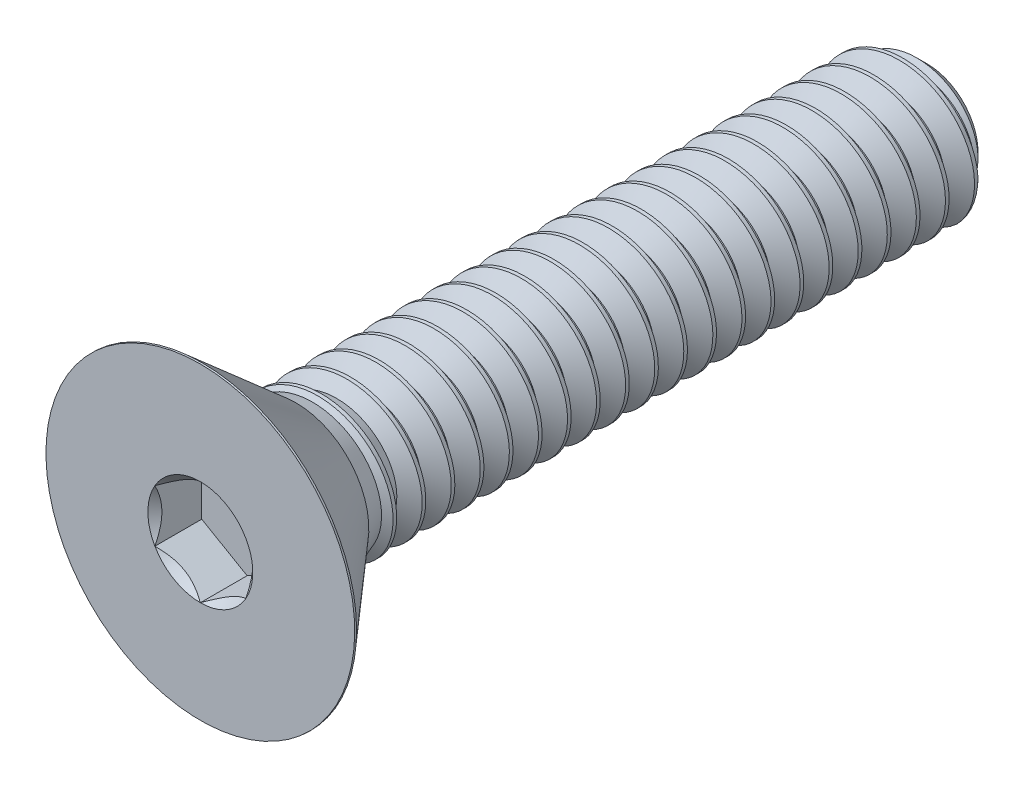
SolidWorks part; units mm, degrees
material "AISI 1020"
ref_plane "Front Plane" through (0, 0, 0) normal (0, 0, 1) x (1, 0, 0)
ref_plane "Top Plane" through (0, 0, 0) normal (0, 1, 0) x (1, 0, 0)
ref_plane "Right Plane" through (0, 0, 0) normal (1, 0, 0) x (0, 0, -1)
sketch "Sketch1" plane through (0, 0, 0) normal (1, 0, 0) x (0, 0, -1)
  line L0 (-15.875, 0) -> (15.875, 0) construction
  line L1 (-15.875, 0) -> (-15.875, 6.7437)
  line L2 (-15.875, 6.7437) -> (-15.7932, 6.7437)
  line L3 (-15.7932, 6.7437) -> (-11.7856, 3.2599)
  line L4 (-15.7932, -6.7437) -> (-11.7856, -3.2599)
  line L5 (15.875, 0) -> (15.875, 3.175)
  line L6 (15.875, 3.175) -> (-11.7856, 3.175)
  line L7 (14.9225, 3.175) -> (15.875, 2.2225)
  line L8 (15.7956, 3.3125) -> (16.4306, 2.2126) construction
  line L9 (16.4306, 2.2126) -> (17.0656, 3.3125) construction
  line L10 (17.0656, 3.3125) -> (15.7956, 3.3125) construction
  line L11 (15.8353, 3.2437) -> (17.0259, 3.2437)
  line L12 (17.0259, 3.2437) -> (16.51, 2.3501)
  line L13 (16.51, 2.3501) -> (16.3512, 2.3501)
  line L14 (16.3512, 2.3501) -> (15.8353, 3.2437)
  line L15 (16.4306, 2.3501) -> (16.4306, 2.2126) construction
  line L16 (15.875, 3.175) -> (16.9862, 3.175) construction
  line L17 (16.4306, 3.3125) -> (16.4306, 3.175) construction
  line L18 (15.875, -3.175) -> (-11.7856, -3.175)
  arc A0 (-11.7856, 3.2599) -> (-11.5584, 3.175) centre (-11.5584, 3.5213) ccw
  point P2 (0, 0)
  point P23 (-13.8303, 0)
  point P27 (16.4306, 3.2437)
  point P30 (13.97, -3.175)
  point P31 (-11.7856, 6.7437)
  point P33 (-11.7856, -6.7437)
  point P34 (-15.7932, -6.7437)
  dimension "Length" = 31.75
  dimension "Head Height" = 4.0894
  dimension "Head Diameter" = 13.4874
  dimension "Countersink Angle" = 82
  dimension "Screw Size Decimal Equivalent" = 6.35
  dimension "Pitch" = 1.27
  dimension "D4" = 0.1588
  dimension "D3" = 45
  dimension "D5" = 0.9525
  dimension "D6" = 2.0447
  dimension "D1" = 1.905
  dimension "D7" = 0.0818
sketch "Sketch8" plane through (0, 0, 0) normal (0, 0, 1) x (1, 0, 0)
  line L1 (0, 2.2914) -> (-1.9844, 1.1457)
  line L2 (-1.9844, 1.1457) -> (-1.9844, -1.1457)
  line L3 (-1.9844, -1.1457) -> (0, -2.2914)
  line L4 (0, -2.2914) -> (1.9844, -1.1457)
  line L5 (1.9844, -1.1457) -> (1.9844, 1.1457)
  line L6 (1.9844, 1.1457) -> (0, 2.2914)
  circle A0 centre (0, 0) radius 1.9844 construction
  dimension "Drive Size" = 3.9688
sketch "Sketch2" plane through (0, 0, 0) normal (1, 0, 0) x (0, 0, -1)
  line L0 (-15.7932, 6.7437) -> (-11.7856, 3.2599) construction
  line L1 (-15.875, 0) -> (-15.875, 6.7437) construction
  line L2 (-15.7932, 6.7437) -> (-11.6879, 3.175)
  line L3 (-15.875, 0) -> (-15.875, 6.7437)
  line L4 (-15.875, 6.7437) -> (-15.7932, 6.7437) construction
  line L5 (-15.875, 6.7437) -> (-15.7932, 6.7437)
  line L6 (-11.6879, 3.175) -> (14.9225, 3.175)
  line L7 (14.9225, 3.175) -> (15.875, 2.2225)
  line L8 (15.875, 2.2225) -> (15.875, 0)
  line L9 (15.875, 0) -> (-15.875, 0)
revolve "Revolve1" add sketch "Sketch2" angle 360 about L9
sketch "Sketch9" plane through (0, 0, 15.875) normal (0, 0, 1) x (1, 0, 0)
  line L0 (1.9844, -1.1457) -> (1.9844, 1.1457) construction
  line L1 (0, -2.2914) -> (1.9844, -1.1457) construction
  line L2 (-1.9844, -1.1457) -> (0, -2.2914) construction
  line L3 (-1.9844, 1.1457) -> (-1.9844, -1.1457) construction
  line L4 (0, 2.2914) -> (-1.9844, 1.1457) construction
  line L5 (1.9844, 1.1457) -> (0, 2.2914) construction
  line L6 (1.9844, -1.1457) -> (1.9844, 1.1457)
  line L7 (0, -2.2914) -> (1.9844, -1.1457)
  line L8 (-1.9844, -1.1457) -> (0, -2.2914)
  line L9 (-1.9844, 1.1457) -> (-1.9844, -1.1457)
  line L10 (0, 2.2914) -> (-1.9844, 1.1457)
  line L11 (1.9844, 1.1457) -> (0, 2.2914)
sketch "Sketch10" plane through (0, 0, 15.875) normal (0, 0, 1) x (1, 0, 0)
  circle A0 centre (0, 0) radius 2.2914
extrude "Cut-Extrude2" cut sketch "Sketch10" against normal up to vertex (2.0447 mm away) draft 45 up to point (0, 0, 13.8303)
extrude "Cut-Extrude1" cut sketch "Sketch9" against normal up to vertex (2.0447 mm away) up to point (0, 0, 13.8303)
ref_plane "Plane1" through (0, 0, 11.6879) normal (0, 0, 1) x (1, 0, 0)
split "Split1" trim tools "Plane1" bodies to split 111 resulting bodies 105 106
sketch "Sketch3" plane through (0, 0, -15.875) normal (0, 0, -1) x (-1, 0, 0)
  circle A0 centre (0, 0) radius 3.175 construction
  circle A1 centre (0, 0) radius 3.175
curve "Helix/Spiral1" pitch 1.27 height 31.75 turns 25
sketch "Sketch4" plane through (0, 0, 0) normal (1, 0, 0) x (0, 0, -1)
  line L0 (15.8353, 3.2437) -> (17.0259, 3.2437) construction
  line L1 (16.3512, 2.3501) -> (15.8353, 3.2437) construction
  line L2 (16.51, 2.3501) -> (16.3512, 2.3501) construction
  line L3 (17.0259, 3.2437) -> (16.51, 2.3501) construction
  line L4 (15.8353, 3.2437) -> (17.0259, 3.2437)
  line L5 (16.3512, 2.3501) -> (15.8353, 3.2437)
  line L6 (16.51, 2.3501) -> (16.3512, 2.3501)
  line L7 (17.0259, 3.2437) -> (16.51, 2.3501)
sweep "Cut-Sweep1" cut profiles "Sketch4" path "Helix/Spiral1"
sketch "Sketch7" plane through (0, 0, 11.6879) normal (0, 0, 1) x (1, 0, 0)
  circle A0 centre (0, 0) radius 3.175
extrude "Boss-Extrude2" add sketch "Sketch7" against normal up to next draft 20
equation "\"D4@Sketch1\" = \"Pitch@Sketch1\" / 8"
equation "\"D5@Sketch1\"=\"Pitch@Sketch1\"*0.75"
equation "\"D4@Helix/Spiral1\"=\"Pitch@Sketch1\""
equation "\"D3@Helix/Spiral1\"=\"Length@Sketch1\""
equation "\"D6@Sketch1\"=\"Head Height@Sketch1\"/2"
equation "\"D1@Sketch1\"=\"Pitch@Sketch1\"*1.5"
equation "\"D7@Sketch1\"=\"Head Height@Sketch1\"*0.02"
